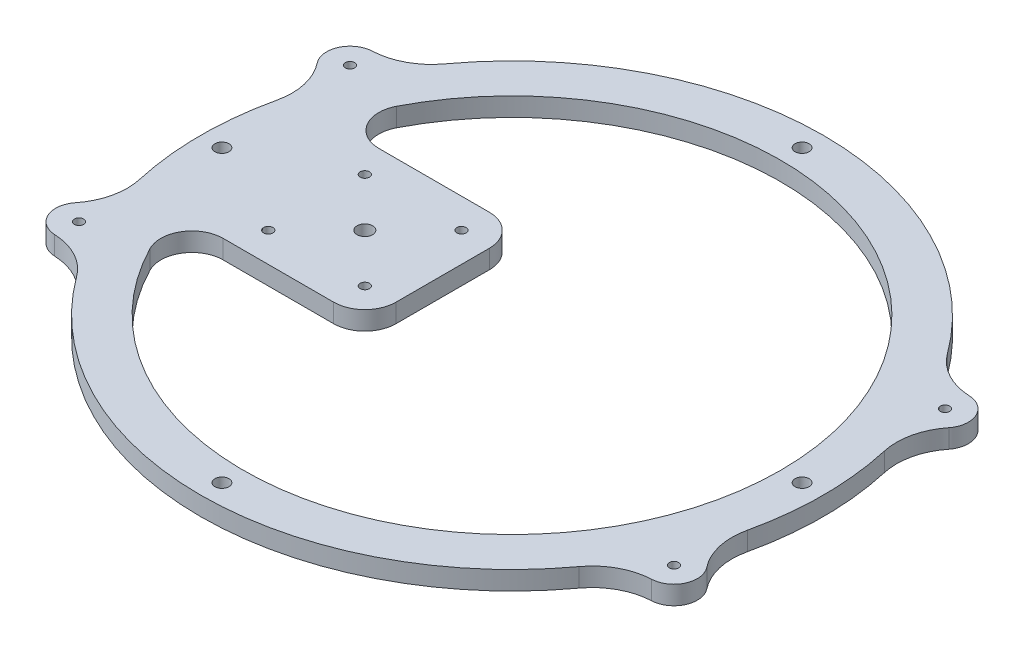
SolidWorks part; units mm, degrees
ref_plane "Front Plane" through (0, 0, 0) normal (0, 0, 1) x (1, 0, 0)
ref_plane "Top Plane" through (0, 0, 0) normal (0, 1, 0) x (1, 0, 0)
ref_plane "Right Plane" through (0, 0, 0) normal (1, 0, 0) x (0, 0, -1)
sketch "Sketch1" plane through (0, 0, 0) normal (0, 1, 0) x (1, 0, 0)
  line L0 (75.9934, 65) -> (110, 65)
  line L1 (-110, 65) -> (-75.9934, 65)
  line L2 (-110, 65) -> (-110, -65)
  line L3 (-110, -65) -> (-75.9934, -65)
  line L4 (110, 65) -> (110, -65)
  line L5 (-110, 65) -> (110, -65) construction
  line L6 (-110, -65) -> (110, 65) construction
  line L7 (75.9934, -65) -> (110, -65)
  circle A0 centre (0, 0) radius 86.25
  arc A3 (-75.9934, -65) -> (75.9934, -65) centre (0, 0) ccw
  arc A4 (75.9934, 65) -> (-75.9934, 65) centre (0, 0) ccw
  point P0 (0, 0)
  dimension "D3" = 172.5
  dimension "D5" = 200
  dimension "D1" = 220
  dimension "D2" = 130
extrude "Boss-Extrude1" add sketch "Sketch1" along normal blind 6
sketch "Sketch2" plane through (0, 0, 0) normal (0, 1, 0) x (1, 0, 0)
  line L0 (0, -3.3) -> (0, 3.3) construction
  line L1 (-3.3, 0) -> (3.3, 0) construction
  circle A0 centre (-95.5, 43.5) radius 1.5
  circle A1 centre (95.5, 43.5) radius 1.5
  circle A2 centre (95.5, -43.5) radius 1.5
  circle A3 centre (-95.5, -43.5) radius 1.5
  dimension "D1" = 3
  dimension "D2" = 95.5
  dimension "D3" = 43.5
extrude "Cut-Extrude1" cut sketch "Sketch2" along normal blind 6
sketch "Sketch3" plane through (0, 0, 0) normal (0, 1, 0) x (1, 0, 0)
  circle A1 centre (0, 93.125) radius 2.25
  circle A2 centre (93.125, 0) radius 2.25
  circle A3 centre (0, -93.125) radius 2.25
  circle A4 centre (-93.125, 0) radius 2.25
  point P13 (0, 0)
  dimension "D1" = 4.5
  dimension "D2" = 93.125
  dimension "D3" = 4
extrude "Cut-Extrude2" cut sketch "Sketch3" along normal blind 6
sketch "Sketch4" plane through (0, 0, 0) normal (0, 1, 0) x (1, 0, 0)
  line L1 (0, -3.3) -> (0, 3.3) construction
  line L6 (98.6089, -36.6747) -> (93.8566, -34.51)
  line L11 (-95.5, 43.5) -> (0, 0) construction
  line L12 (-98.6089, 36.6747) -> (-93.8566, 34.51)
  line L13 (-92.3911, 50.3253) -> (-87.6388, 48.1606)
  line L14 (92.3911, -50.3253) -> (87.6388, -48.1606)
  line L15 (75.9934, -65) -> (110, -65)
  line L16 (-75.9934, 65) -> (-110, 65)
  line L17 (-110, 65) -> (-110, -65)
  line L18 (110, 65) -> (110, -65)
  line L20 (-3.3, 0) -> (3.3, 0) construction
  line L21 (-75.9934, -65) -> (-110, -65)
  line L22 (-92.3911, -50.3253) -> (-87.6388, -48.1606)
  line L23 (-98.6089, -36.6747) -> (-93.8566, -34.51)
  line L24 (75.9934, 65) -> (110, 65)
  line L25 (92.3911, 50.3253) -> (87.6388, 48.1606)
  line L26 (98.6089, 36.6747) -> (93.8566, 34.51)
  arc A0 (75.9934, -65) -> (87.6388, -48.1606) centre (0, 0) ccw
  arc A1 (-75.9934, 65) -> (-87.6388, 48.1606) centre (0, 0) ccw
  arc A2 (-92.3911, 50.3253) -> (-98.6089, 36.6747) centre (-95.5, 43.5) ccw
  arc A3 (-93.8566, 34.51) -> (-93.8566, -34.51) centre (0, 0) ccw
  arc A4 (-92.3911, -50.3253) -> (-98.6089, -36.6747) centre (-95.5, -43.5) cw
  arc A5 (-75.9934, -65) -> (-87.6388, -48.1606) centre (0, 0) cw
  arc A6 (92.3911, -50.3253) -> (98.6089, -36.6747) centre (95.5, -43.5) ccw
  arc A7 (93.8566, 34.51) -> (93.8566, -34.51) centre (0, 0) cw
  arc A8 (92.3911, 50.3253) -> (98.6089, 36.6747) centre (95.5, 43.5) cw
  arc A9 (75.9934, 65) -> (87.6388, 48.1606) centre (0, 0) cw
  dimension "D1" = 100
  dimension "D2" = 7.5
  dimension "D3" = 7.5
extrude "Cut-Extrude3" cut sketch "Sketch4" along normal blind 6
fillet "Fillet1" radius 20 8 edges at (87.6388, 3, -48.1606) (93.8566, 3, -34.51) (93.8566, 3, 34.51) (87.6388, 3, 48.1606) (-87.6388, 3, 48.1606) (-93.8566, 3, 34.51) (-93.8566, 3, -34.51) (-87.6388, 3, -48.1606)
sketch "Sketch5" plane through (0, 0, 0) normal (0, 1, 0) x (1, 0, 0)
  line L0 (-47.25, 0) -> (0, 0) construction
  line L1 (-62.75, 15.5) -> (-31.75, 15.5) construction
  line L2 (-62.75, 15.5) -> (-62.75, -15.5) construction
  line L3 (-62.75, -15.5) -> (-31.75, -15.5) construction
  line L4 (-31.75, 15.5) -> (-31.75, -15.5) construction
  line L5 (-72.25, 25) -> (-22.25, 25)
  line L7 (-72.25, -25) -> (-22.25, -25)
  line L8 (-22.25, 25) -> (-22.25, -25)
  line L9 (-72.25, 25) -> (-22.25, -25) construction
  line L10 (-72.25, -25) -> (-22.25, 25) construction
  line L11 (-72.25, 25) -> (-87.6894, 25)
  line L13 (-72.25, -25) -> (-87.6894, -25)
  line L14 (-87.6894, 25) -> (-87.6894, -25)
  circle A0 centre (-47.25, 0) radius 2.5
  circle A1 centre (-62.75, 15.5) radius 1.5
  circle A2 centre (-31.75, 15.5) radius 1.5
  circle A3 centre (-62.75, -15.5) radius 1.5
  circle A4 centre (-31.75, -15.5) radius 1.5
  dimension "D2" = 5
  dimension "D3" = 3
  dimension "D4" = 3
  dimension "D5" = 3
  dimension "D6" = 3
  dimension "D7" = 31
  dimension "D8" = 15.5
  dimension "D9" = 15.5
  dimension "D10" = 50
  dimension "D1" = 47.25
  dimension "D11" = 50
  dimension "D12" = 25
  dimension "D13" = 87.6894
extrude "Boss-Extrude2" add sketch "Sketch5" along normal blind 6
fillet "Fillet2" radius 10 4 edges at (-82.5473, 3, -25) (-82.5473, 3, 25) (-22.25, 3, -25) (-22.25, 3, 25)
